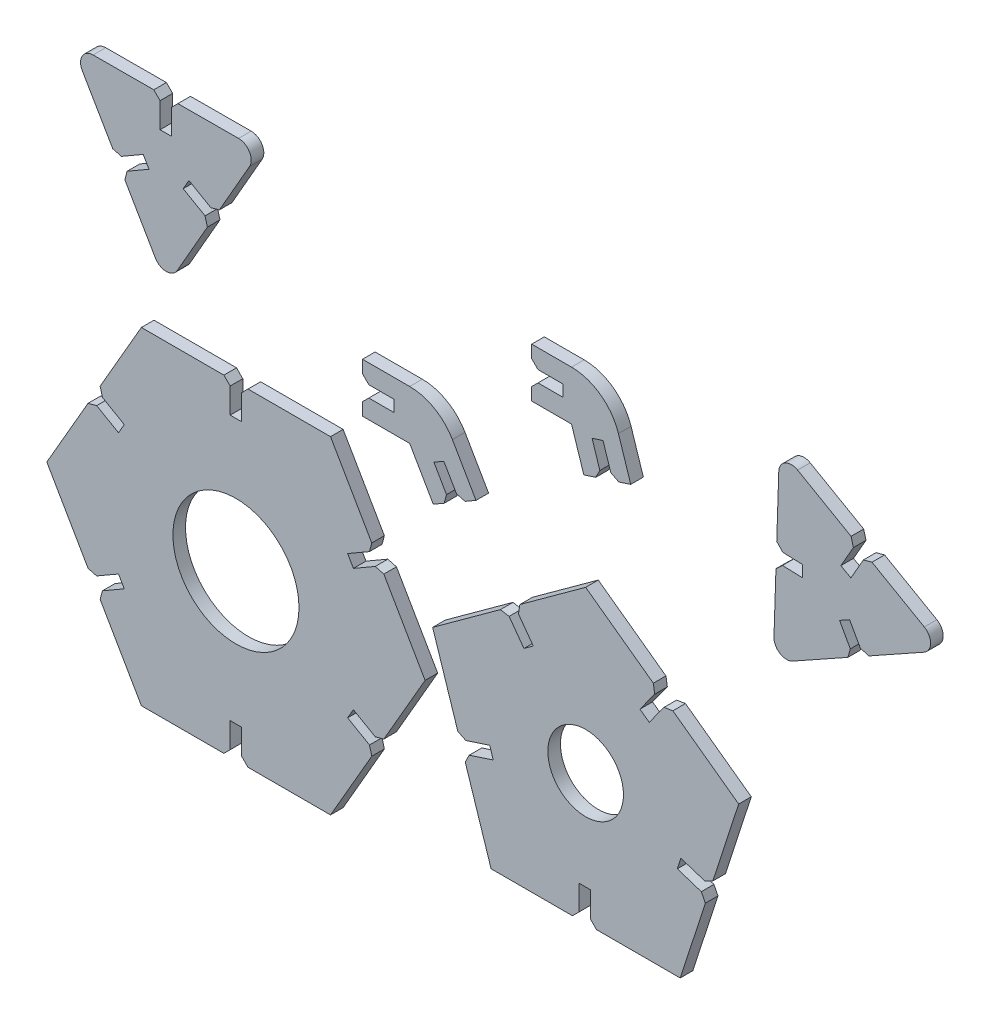
SolidWorks part; units mm, degrees
ref_plane "Alzado" through (0, 0, 0) normal (0, 0, 1) x (1, 0, 0)
ref_plane "Planta" through (0, 0, 0) normal (0, 1, 0) x (1, 0, 0)
ref_plane "Vista lateral" through (0, 0, 0) normal (1, 0, 0) x (0, 0, -1)
sketch "Croquis1" plane through (0, 0, 0) normal (0, 0, 1) x (1, 0, 0)
  line L0 (-22.4988, 34.6927) -> (-16.6209, 26.6026)
  line L1 (0, 51.039) -> (-22.4988, 34.6927)
  line L2 (-48.541, 15.7719) -> (-39.9473, -10.6769)
  line L3 (-30, -41.2915) -> (-2.19, -41.2915)
  line L4 (30, -41.2915) -> (38.5938, -14.8426)
  line L5 (48.541, 15.7719) -> (26.0423, 32.1182)
  line L12 (26.0423, 32.1182) -> (20.1644, 24.0281)
  line L13 (-23.9752, 33.62) -> (-18.0974, 25.5299) construction
  line L14 (-25.4517, 32.5473) -> (-19.5738, 24.4572)
  line L15 (-19.5738, 24.4572) -> (-16.6209, 26.6026)
  line L16 (-25.4517, 32.5473) -> (-48.541, 15.7719)
  line L17 (23.0893, 34.2637) -> (17.2115, 26.1735)
  line L18 (17.2115, 26.1735) -> (20.1644, 24.0281)
  line L19 (24.5658, 33.1909) -> (18.6879, 25.1008) construction
  line L20 (38.5938, -14.8426) -> (29.0832, -11.7524)
  line L21 (39.7217, -11.3712) -> (30.2111, -8.281)
  line L22 (30.2111, -8.281) -> (29.0832, -11.7524)
  line L23 (39.1577, -13.1069) -> (29.6472, -10.0167) construction
  line L24 (-2.19, -41.2915) -> (-2.19, -31.2915)
  line L25 (1.46, -41.2915) -> (1.46, -31.2915)
  line L26 (1.46, -31.2915) -> (-2.19, -31.2915)
  line L27 (-0.365, -41.2915) -> (-0.365, -31.2915) construction
  line L28 (-39.9473, -10.6769) -> (-30.4367, -7.5868)
  line L29 (-38.8193, -14.1483) -> (-29.3088, -11.0581)
  line L30 (-29.3088, -11.0581) -> (-30.4367, -7.5868)
  line L31 (-39.3833, -12.4126) -> (-29.8727, -9.3225) construction
  line L32 (23.0893, 34.2637) -> (0, 51.039)
  line L33 (39.7217, -11.3712) -> (48.541, 15.7719)
  line L34 (1.46, -41.2915) -> (30, -41.2915)
  line L35 (-38.8193, -14.1483) -> (-30, -41.2915)
  arc A0 (-25.4365, 32.5264) -> (-39.892, -10.659) centre (0, 0) ccw construction
  arc A1 (23.0742, 34.2428) -> (-22.4646, 34.6457) centre (0, 0) ccw construction
  arc A2 (39.6971, -11.3632) -> (26.0081, 32.0712) centre (0, 0) ccw construction
  arc A3 (1.46, -41.2656) -> (38.5385, -14.8246) centre (0, 0) ccw construction
  arc A4 (-38.7948, -14.1403) -> (-2.19, -41.2333) centre (0, 0) ccw construction
  point P1 (-18.0974, 25.5299)
  point P19 (18.6879, 25.1008)
  point P26 (29.6472, -10.0167)
  point P33 (-0.365, -31.2915)
  point P40 (-29.8727, -9.3225)
  point P47 (0, 0)
extrude "Saliente-Extruir1" add sketch "Croquis1" along normal blind 4
chamfer "Chaflán1" distance 2 angle 45 10 edges at (-38.8193, -14.1483, 2) (-39.9473, -10.6769, 2) (-25.4517, 32.5473, 2) (-22.4988, 34.6927, 2) (-2.19, -41.2915, 2) (1.46, -41.2915, 2) (38.5938, -14.8426, 2) (39.7217, -11.3712, 2) (26.0423, 32.1182, 2) (23.0893, 34.2637, 2)
sketch "Croquis2" plane through (0, 0, 0) normal (0, 0, 1) x (1, 0, 0)
  line L0 (55, 0) -> (-55, 0) construction
  line L1 (-50.9358, 0) -> (-65.0233, 24.4003)
  line L2 (-80.9358, 51.9615) -> (-109.1108, 51.9615)
  line L3 (-140.9358, 51.9615) -> (-155.0233, 27.5613)
  line L4 (-170.9358, 0) -> (-156.8483, -24.4003)
  line L5 (-140.9358, -51.9615) -> (-112.7608, -51.9615)
  line L6 (-80.9358, -51.9615) -> (-66.8483, -27.5613)
  line L7 (-110.9358, 0) -> (-110.9358, 43.3013) construction
  line L8 (-112.7608, 51.9615) -> (-112.7608, 41.9615)
  line L9 (-112.7608, 41.9615) -> (-109.1108, 41.9615)
  line L10 (-109.1108, 41.9615) -> (-109.1108, 51.9615)
  line L11 (-112.7608, 51.9615) -> (-140.9358, 51.9615)
  line L12 (-66.8483, 27.5613) -> (-75.5085, 22.5613)
  line L13 (-75.5085, 22.5613) -> (-73.6835, 19.4003)
  line L14 (-73.6835, 19.4003) -> (-65.0233, 24.4003)
  line L15 (-65.0233, -24.4003) -> (-73.6835, -19.4003)
  line L16 (-73.6835, -19.4003) -> (-75.5085, -22.5613)
  line L17 (-75.5085, -22.5613) -> (-66.8483, -27.5613)
  line L18 (-109.1108, -51.9615) -> (-109.1108, -41.9615)
  line L19 (-109.1108, -41.9615) -> (-112.7608, -41.9615)
  line L20 (-112.7608, -41.9615) -> (-112.7608, -51.9615)
  line L21 (-155.0233, -27.5613) -> (-146.363, -22.5613)
  line L22 (-146.363, -22.5613) -> (-148.188, -19.4003)
  line L23 (-148.188, -19.4003) -> (-156.8483, -24.4003)
  line L24 (-156.8483, 24.4003) -> (-148.188, 19.4003)
  line L25 (-148.188, 19.4003) -> (-146.363, 22.5613)
  line L26 (-146.363, 22.5613) -> (-155.0233, 27.5613)
  line L27 (-156.8483, 24.4003) -> (-170.9358, 0)
  line L28 (-155.0233, -27.5613) -> (-140.9358, -51.9615)
  line L29 (-109.1108, -51.9615) -> (-80.9358, -51.9615)
  line L30 (-65.0233, -24.4003) -> (-50.9358, 0)
  line L31 (-66.8483, 27.5613) -> (-80.9358, 51.9615)
  arc A0 (-112.7608, 51.9295) -> (-154.9955, 27.5452) centre (-110.9358, 0) ccw construction
  arc A1 (-156.8205, 24.3842) -> (-156.8205, -24.3842) centre (-110.9358, 0) ccw construction
  arc A2 (-154.9955, -27.5452) -> (-112.7608, -51.9295) centre (-110.9358, 0) ccw construction
  arc A3 (-109.1108, -51.9295) -> (-66.876, -27.5452) centre (-110.9358, 0) ccw construction
  arc A4 (-65.051, -24.3842) -> (-65.051, 24.3842) centre (-110.9358, 0) ccw construction
  arc A5 (-66.876, 27.5452) -> (-109.1108, 51.9295) centre (-110.9358, 0) ccw construction
  point P13 (-110.9358, 41.9615)
  point P40 (-110.9358, 0)
extrude "Saliente-Extruir2" add sketch "Croquis2" along normal blind 4 separate body
chamfer "Chaflán2" distance 2 angle 45 12 edges at (-155.0233, 27.5613, 2) (-156.8483, 24.4003, 2) (-156.8483, -24.4003, 2) (-155.0233, -27.5613, 2) (-109.1108, -51.9615, 2) (-112.7608, -51.9615, 2) (-65.0233, -24.4003, 2) (-66.8483, -27.5613, 2) (-65.0233, 24.4003, 2) (-66.8483, 27.5613, 2) (-109.1108, 51.9615, 2) (-112.7608, 51.9615, 2)
sketch "Croquis3" plane through (0, 0, 0) normal (0, 0, 1) x (1, 0, 0)
  line L0 (-70.7863, 78.3052) -> (-46.7863, 78.3052)
  line L1 (-46.7863, 78.3052) -> (-34.7863, 57.5206)
  line L2 (-70.7863, 62.6552) -> (-55.8218, 62.6552)
  line L3 (-55.8218, 62.6552) -> (-48.3396, 49.6956)
  line L4 (-70.7863, 78.3052) -> (-70.7863, 72.3052)
  line L5 (-48.3396, 49.6956) -> (-43.1434, 52.6956)
  line L6 (-70.7863, 72.3052) -> (-60.7863, 72.3052)
  line L7 (-60.7863, 72.3052) -> (-60.7863, 68.6552)
  line L8 (-60.7863, 68.6552) -> (-70.7863, 68.6552)
  line L9 (-43.1434, 52.6956) -> (-48.1434, 61.3558)
  line L10 (-48.1434, 61.3558) -> (-44.9824, 63.1808)
  line L11 (-44.9824, 63.1808) -> (-39.9824, 54.5206)
  line L14 (-39.9824, 54.5206) -> (-34.7863, 57.5206)
  line L15 (-70.7863, 68.6552) -> (-70.7863, 62.6552)
extrude "Saliente-Extruir3" add sketch "Croquis3" along normal blind 4 separate body
chamfer "Chaflán3" distance 2 angle 45 4 edges at (-43.1434, 52.6956, 2) (-39.9824, 54.5206, 2) (-70.7863, 68.6552, 2) (-70.7863, 72.3052, 2)
fillet "Redondeo1" radius 15.65 1 edges at (-46.7863, 78.3052, 2)
sketch "Croquis4" plane through (0, 0, 0) normal (0, 0, 1) x (1, 0, 0)
  line L0 (-17.1152, 109.2922) -> (6.8848, 109.2922)
  line L1 (6.8848, 109.2922) -> (14.3012, 86.4668)
  line L2 (-17.1152, 93.6422) -> (-4.4856, 93.6422)
  line L3 (-4.4856, 93.6422) -> (-0.5829, 81.6307)
  line L4 (-17.1152, 109.2922) -> (-17.1152, 103.2922)
  line L5 (-0.5829, 81.6307) -> (5.1235, 83.4848)
  line L6 (-17.1152, 103.2922) -> (-7.1152, 103.2922)
  line L7 (-7.1152, 103.2922) -> (-7.1152, 99.6422)
  line L8 (-7.1152, 99.6422) -> (-17.1152, 99.6422)
  line L9 (5.1235, 83.4848) -> (2.0333, 92.9954)
  line L10 (2.0333, 92.9954) -> (5.5047, 94.1233)
  line L11 (5.5047, 94.1233) -> (8.5948, 84.6127)
  line L14 (8.5948, 84.6127) -> (14.3012, 86.4668)
  line L15 (-17.1152, 99.6422) -> (-17.1152, 93.6422)
extrude "Saliente-Extruir4" add sketch "Croquis4" along normal blind 4 separate body
fillet "Redondeo2" radius 15.65 1 edges at (6.8848, 109.2922, 2)
chamfer "Chaflán4" distance 2 angle 45 4 edges at (8.5948, 84.6127, 2) (5.1235, 83.4848, 2) (-17.1152, 99.6422, 2) (-17.1152, 103.2922, 2)
sketch "Croquis5" plane through (0, 0, 4) normal (0, 0, 1) x (1, 0, 0)
  line L0 (55, 0) -> (-55, 0) construction
  circle A0 centre (-110.9358, 0) radius 20
  circle A1 centre (-110.9358, 0) radius 60 construction
  circle A2 centre (0, 0) radius 12
extrude "Cortar-Extruir1" cut sketch "Croquis5" against normal blind 4
sketch "Croquis8" plane through (0, 0, 0) normal (0, 0, 1) x (1, 0, 0)
  line L0 (-163.1806, 119.1389) -> (-149.0134, 94.7846)
  line L1 (-103.1806, 119.3349) -> (-131.3556, 119.2429)
  line L7 (-133.0108, 67.2754) -> (-119.003, 91.7217)
  line L8 (-133.0108, 67.2754) -> (-132.7811, 109.2429) construction
  line L9 (-135.0056, 119.2309) -> (-135.0056, 109.2429)
  line L10 (-135.0056, 109.2429) -> (-131.3556, 109.2429)
  line L11 (-131.3556, 109.2429) -> (-131.3556, 119.2429)
  line L12 (-135.0056, 119.2309) -> (-163.1806, 119.1389)
  line L13 (-127.6633, 96.7217) -> (-119.003, 91.7217)
  line L14 (-117.1884, 94.8886) -> (-125.8383, 99.8827)
  line L15 (-125.8383, 99.8827) -> (-127.6633, 96.7217)
  line L16 (-140.3531, 99.7846) -> (-149.0134, 94.7846)
  line L17 (-147.178, 91.6296) -> (-138.5281, 96.6237)
  line L18 (-138.5281, 96.6237) -> (-140.3531, 99.7846)
  line L19 (-147.178, 91.6296) -> (-133.0108, 67.2754)
  line L20 (-117.1884, 94.8886) -> (-103.1806, 119.3349)
  circle A0 centre (-133.124, 101.9164) radius 34.6412 construction
  point P20 (-133.124, 101.9164)
extrude "Saliente-Extruir6" add sketch "Croquis8" along normal blind 4 separate body
fillet "Redondeo4" radius 4 3 edges at (-133.0108, 67.2754, 2) (-163.1806, 119.1389, 2) (-103.1806, 119.3349, 2)
sketch "Croquis7" plane through (0, 0, 0) normal (0, 0, 1) x (1, 0, 0)
  line L0 (61.4776, 120.1589) -> (60.5503, 91.979)
  line L6 (113.549, 90.35) -> (89.0971, 104.3477)
  line L7 (59.503, 60.1512) -> (84.9328, 74.3604)
  line L8 (87.5133, 105.2544) -> (78.5297, 89.5614) construction
  line L13 (78.5297, 89.5614) -> (86.526, 75.2506) construction
  line L14 (78.5297, 89.5614) -> (60.4903, 90.155) construction
  line L15 (85.9295, 106.1611) -> (80.9613, 97.4825)
  line L16 (80.9613, 97.4825) -> (84.129, 95.6692)
  line L17 (84.129, 95.6692) -> (89.0971, 104.3477)
  line L18 (85.9295, 106.1611) -> (61.4776, 120.1589)
  line L19 (84.9328, 74.3604) -> (80.5387, 82.2245)
  line L20 (80.5387, 82.2245) -> (83.725, 84.0049)
  line L21 (83.725, 84.0049) -> (88.1192, 76.1408)
  line L22 (88.1192, 76.1408) -> (113.549, 90.35)
  line L23 (60.5503, 91.979) -> (68.8456, 91.7061)
  line L24 (68.8456, 91.7061) -> (68.7256, 88.058)
  line L25 (68.7256, 88.058) -> (60.4303, 88.331)
  line L26 (60.4303, 88.331) -> (59.503, 60.1512)
  circle A1 centre (78.5297, 89.5614) radius 35.0282 construction
extrude "Saliente-Extruir7" add sketch "Croquis7" along normal blind 4 separate body
fillet "Redondeo5" radius 4 3 edges at (59.503, 60.1512, 2) (113.549, 90.35, 2) (61.4776, 120.1589, 2)
chamfer "Chaflán5" distance 2 angle 45 6 edges at (-147.178, 91.6296, 2) (-149.0134, 94.7846, 2) (-117.1884, 94.8886, 2) (-119.003, 91.7217, 2) (-131.3556, 119.2429, 2) (-135.0056, 119.2309, 2)
chamfer "Chaflán6" distance 2 angle 45 6 edges at (85.9295, 106.1611, 2) (89.0971, 104.3477, 2) (84.9328, 74.3604, 2) (88.1192, 76.1408, 2) (60.4303, 88.331, 2) (60.5503, 91.979, 2)
equation "\"E\"= 4'Espesor del cartón"
equation "\"K\"= 0.075'kerf"
equation "\"P\"= 0.2'press fit"
equation "\"L\"= 10'longitud hueco"
equation "\"A\"= 60'arista"
equation "\"T\"= \"E\" - ( 2 * \"K\" ) - \"P\"'ancho hueco modificado"
equation "\"X\" = \"T\" + 12'Ancho piezas de unión"
equation "\"D4@Croquis1\"=\"L\""
equation "\"D1@Croquis1\"=\"A\""
equation "\"D3@Croquis1\"=\"T\""
equation "\"D1@Saliente-Extruir1\"=\"E\""
equation "\"D1@Chaflán1\"=\"E\"/2"
equation "\"D1@Croquis2\"=\"A\""
equation "\"D2@Croquis2\"=\"T\""
equation "\"D3@Croquis2\"=\"L\""
equation "\"D1@Chaflán2\"=\"E\"/2"
equation "\"Y\"= \"A\" / 2.5'longitud piezas de unión"
equation "\"D3@Croquis3\"=\"Y\""
equation "\"D4@Croquis3\"=\"Y\""
equation "\"D5@Croquis3\"=\"L\""
equation "\"D2@Croquis3\"=\"X\""
equation "\"D6@Croquis3\"=\"T\""
equation "\"D7@Croquis3\"=\"T\""
equation "\"D8@Croquis3\"=\"L\""
equation "\"D1@Saliente-Extruir3\"=\"E\""
equation "\"D1@Saliente-Extruir2\"=\"E\""
equation "\"D1@Chaflán3\"=\"E\"/2"
equation "\"D1@Redondeo1\"=\"X\""
equation "\"D1@Saliente-Extruir4\"=\"E\""
equation "\"D1@Redondeo2\"=\"X\""
equation "\"D1@Chaflán4\"=\"E\"/2"
equation "\"D1@Croquis5\"=\"A\"/1.5"
equation "\"D2@Croquis5\"=\"A\"/2.5"
equation "\"D3@Croquis7\"=\"A\""
equation "\"D8@Croquis4\"=\"L\""
equation "\"D5@Croquis4\"=\"L\""
equation "\"D4@Croquis4\"=\"Y\""
equation "\"D3@Croquis4\"=\"Y\""
equation "\"D2@Croquis4\"=\"X\""
equation "\"D5@Croquis8\"=\"L\""
equation "\"D1@Saliente-Extruir6\"=\"E\""
equation "\"D1@Croquis8\"=\"T\""
equation "\"D2@Croquis8\"=\"A\""
equation "\"D1@Redondeo4\"=\"E\""
equation "\"D4@Croquis7\"=\"T\""
equation "\"D5@Croquis7\"=\"L\""
equation "\"D6@Croquis7\"=\"T\""
equation "\"D7@Croquis7\"=\"T\""
equation "\"D1@Saliente-Extruir7\"=\"E\""
equation "\"D1@Redondeo5\"=\"E\""
equation "\"D1@Chaflán5\"=\"E\"/2"
equation "\"D1@Chaflán6\"=\"E\"/2"
